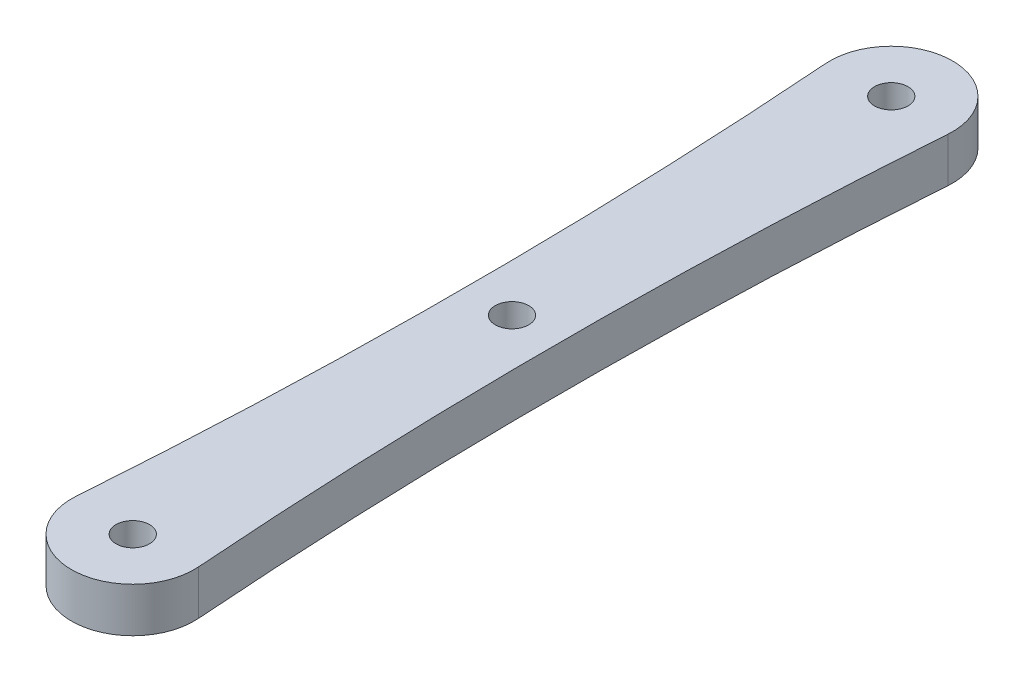
SolidWorks part; units mm, degrees
ref_plane "Front Plane" through (0, 0, 0) normal (0, 0, 1) x (1, 0, 0)
ref_plane "Top Plane" through (0, 0, 0) normal (0, 1, 0) x (1, 0, 0)
ref_plane "Right Plane" through (0, 0, 0) normal (1, 0, 0) x (0, 0, -1)
sketch "Sketch1" plane through (0, 0, 0) normal (0, 1, 0) x (1, 0, 0)
  line L0 (0, 0) -> (0, 68) construction
  line L3 (-4.25, 34) -> (4.25, 34) construction
  circle A2 centre (0, 0) radius 1.5
  circle A3 centre (0, 68) radius 1.5
  arc A8 (-5.4852, 0.4039) -> (5.4852, 0.4039) centre (0, 0) ccw
  arc A9 (5.4852, 67.5961) -> (-5.4852, 67.5961) centre (0, 68) ccw
  arc A10 (-5.4852, 67.5961) -> (-5.4852, 0.4039) centre (-461.775, 34) cw
  arc A11 (5.4852, 67.5961) -> (5.4852, 0.4039) centre (461.775, 34) ccw
  circle A12 centre (0, 34) radius 1.5
  point P3 (0, 34)
  point P16 (-4.25, 34)
  point P19 (4.25, 34)
  point P23 (0, 34)
  dimension "D1" = 3
  dimension "D2" = 68
  dimension "D3" = 4
  dimension "D5" = 3
  dimension "D4" = 8.5
extrude "Boss-Extrude1" add sketch "Sketch1" along normal blind 4
